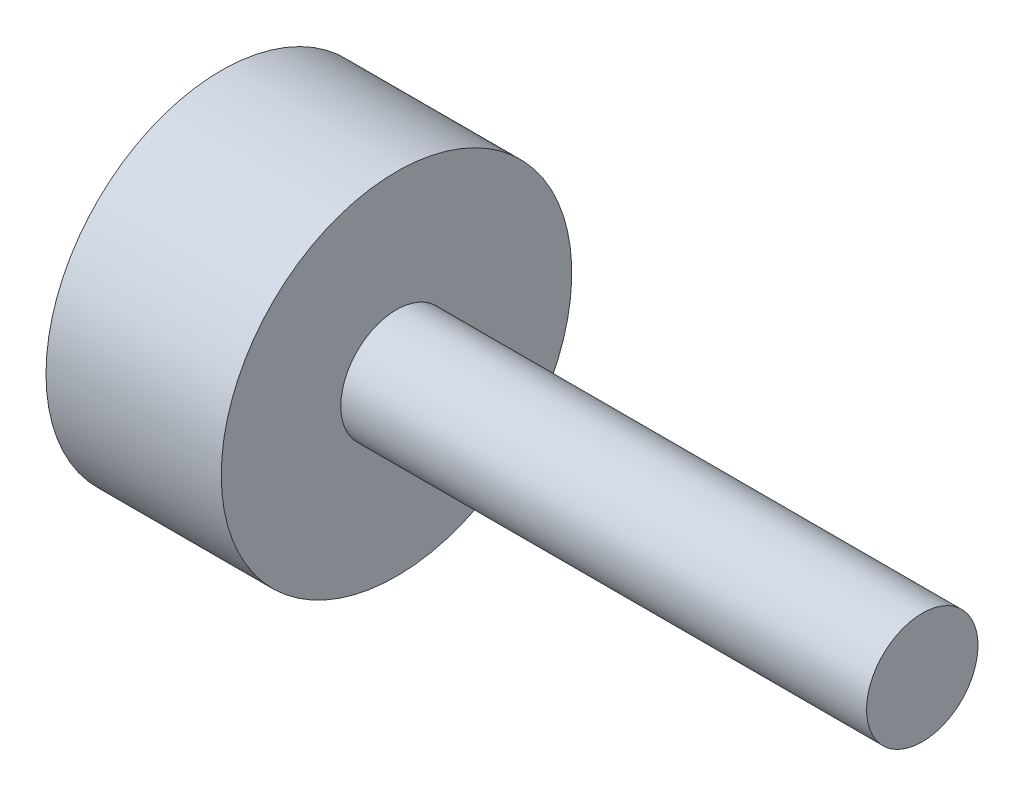
SolidWorks part; units mm, degrees
ref_plane "Plano frontal" through (0, 0, 0) normal (0, 0, 1) x (1, 0, 0)
ref_plane "Plano superior" through (0, 0, 0) normal (0, 1, 0) x (1, 0, 0)
ref_plane "Plano direito" through (0, 0, 0) normal (1, 0, 0) x (0, 0, -1)
sketch "Esboço1" plane through (0, 0, 0) normal (1, 0, 0) x (0, 0, -1)
  circle A0 centre (0, 0) radius 1.59
  dimension "D1" = 3.18
extrude "Ressalto-extrusão1" add sketch "Esboço1" along normal blind 15
sketch "Esboço3" plane through (0, 0, 0) normal (-1, 0, 0) x (0, 0, 1)
  circle A0 centre (0, 0) radius 5
  dimension "D1" = 10
extrude "Ressalto-extrusão5" add sketch "Esboço3" along normal blind 5
sketch "Esboço8" plane through (-5, 0, 0) normal (-1, 0, 0) x (0, 0, 1)
  circle A0 centre (0, 0) radius 1
  dimension "D1" = 2
extrude "Corte-extrusão1" cut sketch "Esboço8" against normal blind 5
